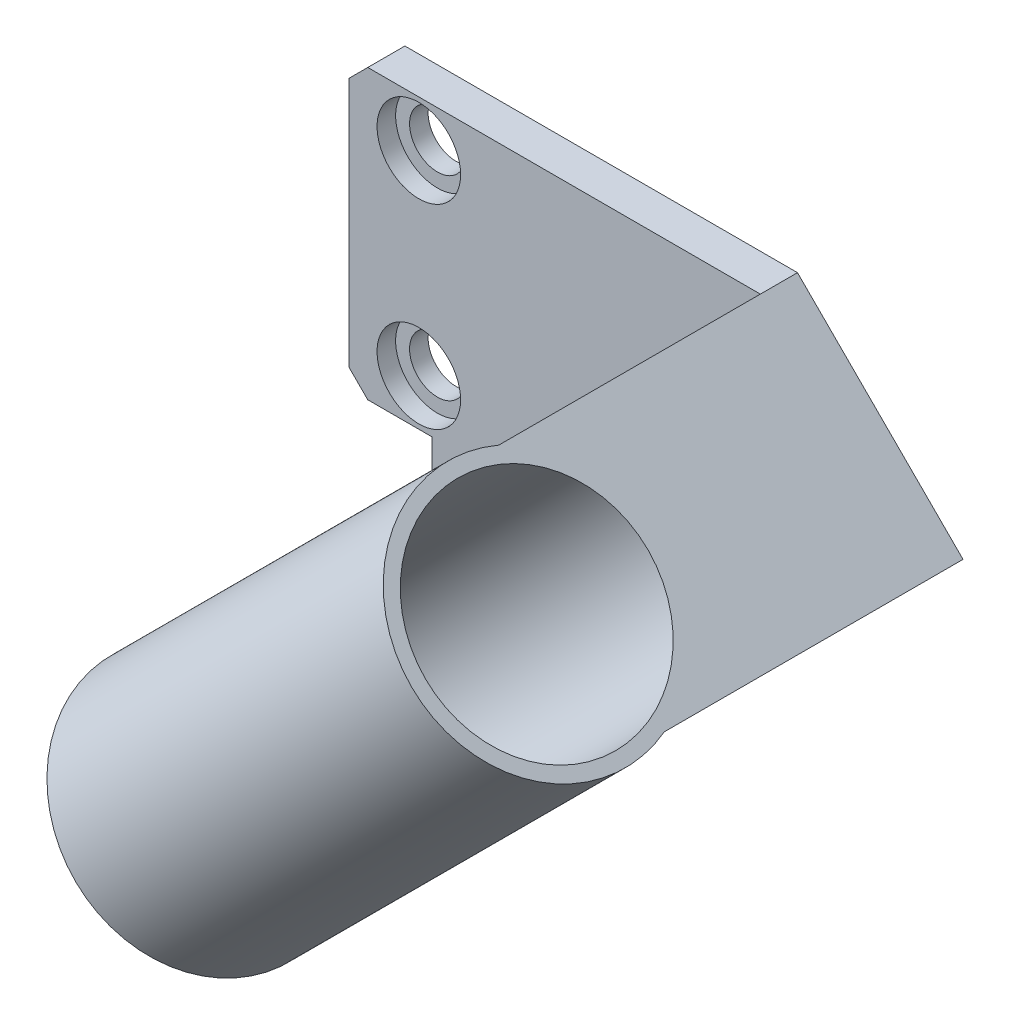
SolidWorks part; units mm, degrees
ref_plane "Front Plane" through (0, 0, 0) normal (0, 0, 1) x (1, 0, 0)
ref_plane "Top Plane" through (0, 0, 0) normal (0, 1, 0) x (1, 0, 0)
ref_plane "Right Plane" through (0, 0, 0) normal (1, 0, 0) x (0, 0, -1)
sketch "Sketch1" plane through (0, 0, 0) normal (0, 0, 1) x (1, 0, 0)
  line L7 (-7.5, -5) -> (7.5, -5)
  line L8 (-7.5, -5) -> (-7.5, 26)
  line L9 (-7.5, 26) -> (7.5, 26)
  line L10 (7.5, -5) -> (7.5, 26)
  line L11 (-7.5, -5) -> (7.5, 26) construction
  line L12 (-7.5, 26) -> (7.5, -5) construction
  circle A0 centre (0, 0) radius 3
  circle A1 centre (0, 21) radius 3
  point P5 (0, 10.5)
  point P6 (0, 0)
  point P8 (0, 10.5)
extrude "Boss-Extrude1" add sketch "Sketch1" along normal blind 4
sketch "Sketch2" plane through (0, 0, 4) normal (0, 0, 1) x (1, 0, 0)
  circle A0 centre (0, 21) radius 4.5
  circle A1 centre (0, 0) radius 4.5
extrude "Cut-Extrude1" cut sketch "Sketch2" against normal blind 2
chamfer "Chamfer1" distance 2 angle 45 2 edges at (-7.5, -5, 2) (-7.5, 26, 2)
sketch "Sketch3" plane through (0, 0, 4) normal (0, 0, 1) x (1, 0, 0)
  line L2 (1.4231, -5) -> (7.5, -5)
  line L3 (1.4231, -11.0769) -> (18.3936, -28.0475)
  line L4 (-45.5, -63) -> (-45.5, -92.4809) construction
  line L10 (18.3936, -28.0475) -> (41.4411, -5)
  line L11 (1.4231, -11.0769) -> (1.4231, -5)
  line L12 (-5.5, -5) -> (7.5, -5) construction
  line L14 (7.5, -5) -> (7.5, 26)
  line L15 (41.4411, -5) -> (54.6118, 8.1707)
  line L16 (54.6118, 8.1707) -> (36.7825, 26)
  line L17 (7.5, 26) -> (36.7825, 26)
extrude "Boss-Extrude3" add sketch "Sketch3" against normal up to surface (4 mm away) up to face at (3, 0, 0)
sketch "Sketch4" plane through (31.3912, 31.3912, 0) normal (0.7071, 0.7071, 0) x (0, 0, -1)
  circle A1 centre (-37, -20.2316) radius 12
  circle A2 centre (-37, -20.2316) radius 13.5
extrude "Boss-Extrude4" add sketch "Sketch4" against normal up to surface (51.2202 mm away) separate body up to face at (9.9083, -19.5622, 2)
sketch "Sketch5" plane through (0, 0, 4) normal (0, 0, 1) x (1, 0, 0)
  line L0 (1.4231, -11.0769) -> (36.7825, 26)
  line L1 (36.7825, 26) -> (54.6118, 8.1707)
  line L2 (54.6118, 8.1707) -> (18.3936, -28.0475)
  line L3 (18.3936, -28.0475) -> (1.4231, -11.0769)
extrude "Boss-Extrude5" add sketch "Sketch5" along normal up to body separate body
